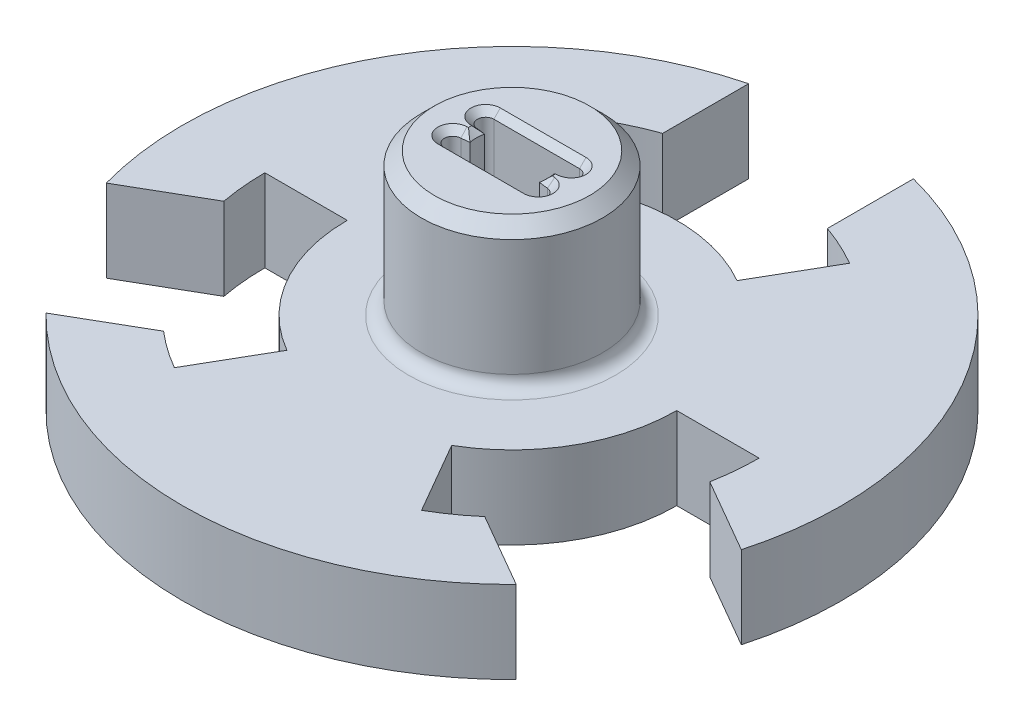
SolidWorks part; units mm, degrees
ref_plane "Front Plane" through (0, 0, 0) normal (0, 0, 1) x (1, 0, 0)
ref_plane "Top Plane" through (0, 0, 0) normal (0, 1, 0) x (1, 0, 0)
ref_plane "Right Plane" through (0, 0, 0) normal (1, 0, 0) x (0, 0, -1)
sketch "Sketch1" plane through (0, 0, 0) normal (0, 1, 0) x (1, 0, 0)
  line L0 (0, -0.5588) -> (0, 0.5588) construction
  line L1 (-2.6727, 0.5588) -> (2.6727, 0.5588) construction
  line L2 (0, 1.905) -> (0, -1.905) construction
  line L3 (-2.6727, -0.5588) -> (2.6727, -0.5588) construction
  line L4 (-3.302, 1.905) -> (3.302, 1.905)
  line L5 (-3.302, -1.905) -> (3.302, -1.905)
  line L6 (-2.6727, 0.5588) -> (-3.3742, 0.6391)
  line L7 (2.6727, 0.5588) -> (3.302, 0.635)
  line L8 (-3.302, -0.635) -> (-2.6727, -0.5588)
  line L9 (2.6727, -0.5588) -> (3.3742, -0.6391)
  arc A0 (2.6727, -0.5588) -> (2.6727, 0.5588) centre (0, 0) ccw
  arc A1 (-2.6727, 0.5588) -> (-2.6727, -0.5588) centre (0, 0) ccw
  circle A2 centre (0, 0) radius 6.985
  arc A3 (3.302, 0.635) -> (3.302, 1.905) centre (3.302, 1.27) ccw
  arc A4 (3.302, -1.905) -> (3.3742, -0.6391) centre (3.302, -1.27) ccw
  arc A5 (-3.302, -0.635) -> (-3.302, -1.905) centre (-3.302, -1.27) ccw
  arc A6 (-3.302, 1.905) -> (-3.3742, 0.6391) centre (-3.302, 1.27) ccw
  point P8 (0, 0)
  point P9 (0, 0.5588)
  point P14 (0, 0)
  dimension "D2" = 5.461
  dimension "D4" = 3.81
  dimension "D5" = 1.27
  dimension "D6" = 1.27
  dimension "D7" = 1.27
  dimension "D11" = 13.97
  dimension "D8" = 1.27
  dimension "D3" = 1.1176
  dimension "D9" = 6.604
  dimension "D10" = 6.604
extrude "Boss-Extrude1" add sketch "Sketch1" along normal blind 10.9966
chamfer "Chamfer5" distance 1 angle 45 1 edges at (0, 10.9966, 6.985)
chamfer "Chamfer6" distance 0.5 angle 45 12 edges at (-3.936, 10.9966, -1.3062) (-3.0235, 10.9966, -0.599) (0, 10.9966, -1.905) (3.937, 10.9966, -1.27) (2.9874, 10.9966, -0.5969) (2.7305, 10.9966, 0) (3.0235, 10.9966, 0.599) (3.936, 10.9966, 1.3062) (0, 10.9966, 1.905) (-3.937, 10.9966, 1.27) (-2.9874, 10.9966, 0.5969) (-2.7305, 10.9966, 0)
sketch "Sketch2" plane through (0, 0, 0) normal (0, -1, 0) x (1, 0, 0)
  line L0 (0, 0) -> (0, 107.6438) construction
  line L1 (0, 0) -> (53.8219, 93.2223) construction
  line L2 (0, 0) -> (93.2223, 53.8219) construction
  line L3 (0, 0) -> (107.6438, 0) construction
  line L4 (0, 0) -> (93.2223, -53.8219) construction
  line L5 (0, 0) -> (53.8219, -93.2223) construction
  line L6 (-6.35, -17.9605) -> (6.35, -17.9605) construction
  line L8 (-6.35, -24.5934) -> (-6.35, -17.9605)
  line L10 (6.35, -24.5934) -> (6.35, -17.9605)
  line L11 (0, 0) -> (0, -107.6438) construction
  line L12 (0, 0) -> (-53.8219, -93.2223) construction
  line L13 (0, 0) -> (-93.2223, -53.8219) construction
  line L14 (0, 0) -> (-107.6438, 0) construction
  line L15 (0, 0) -> (-93.2223, 53.8219) construction
  line L16 (0, 0) -> (-53.8219, 93.2223) construction
  line L17 (-6.35, -10.9985) -> (-9.525, -16.4978)
  line L18 (6.35, -10.9985) -> (9.525, -16.4978)
  line L19 (-18.1235, 17.796) -> (-12.3793, 14.4795)
  line L20 (-6.35, 10.9985) -> (-9.525, 16.4978)
  line L21 (-12.7, 0) -> (-19.05, 0)
  line L22 (-24.4735, 6.7975) -> (-18.7293, 3.481)
  line L23 (24.4735, 6.7975) -> (18.7293, 3.481)
  line L24 (12.7, 0) -> (19.05, 0)
  line L25 (6.35, 10.9985) -> (9.525, 16.4978)
  line L26 (18.1235, 17.796) -> (12.3793, 14.4795)
  circle A23 centre (0, 0) radius 1.0581
  arc A24 (-6.35, -10.9985) -> (6.35, -10.9985) centre (0, 0) ccw
  arc A25 (6.35, -24.5934) -> (24.4735, 6.7975) centre (0, 0) ccw
  arc A26 (6.35, -17.9605) -> (9.525, -16.4978) centre (0, 0) ccw
  arc A27 (-9.525, -16.4978) -> (-6.35, -17.9605) centre (0, 0) ccw
  arc A28 (-9.525, 16.4978) -> (-12.3793, 14.4795) centre (0, 0) ccw
  arc A32 (-24.4735, 6.7975) -> (-6.35, -24.5934) centre (0, 0) ccw
  arc A33 (18.1235, 17.796) -> (-18.1235, 17.796) centre (0, 0) ccw
  arc A34 (-6.35, 10.9985) -> (-12.7, 0) centre (0, 0) ccw
  arc A35 (-18.7293, 3.481) -> (-19.05, 0) centre (0, 0) ccw
  arc A36 (19.05, 0) -> (18.7293, 3.481) centre (0, 0) ccw
  arc A37 (12.7, 0) -> (6.35, 10.9985) centre (0, 0) ccw
  arc A38 (12.3793, 14.4795) -> (9.525, 16.4978) centre (0, 0) ccw
  point P9 (0, 0)
  point P14 (0, 25.4)
  point P23 (0, 12.7)
  point P25 (0, -17.9605)
  point P29 (0, 0)
  point P42 (0, 0)
  point P51 (0, 0)
  dimension "D1" = 50.8
  dimension "D3" = 25.4
  dimension "D4" = 12.7
  dimension "D5" = 38.1
  dimension "D8" = 2.1162
  dimension "D6" = 3
  dimension "D2" = 12
extrude "Boss-Extrude2" add sketch "Sketch2" along normal blind 6.35
fillet "Fillet1" radius 1 1 edges at (0, 0, 6.985)
sketch "Sketch3" plane through (0, -6.35, 0) normal (0, -1, 0) x (1, 0, 0)
  circle A0 centre (0, 0) radius 1.905
  dimension "D1" = 3.81
extrude "Cut-Extrude1" cut sketch "Sketch3" against normal blind 2.54
